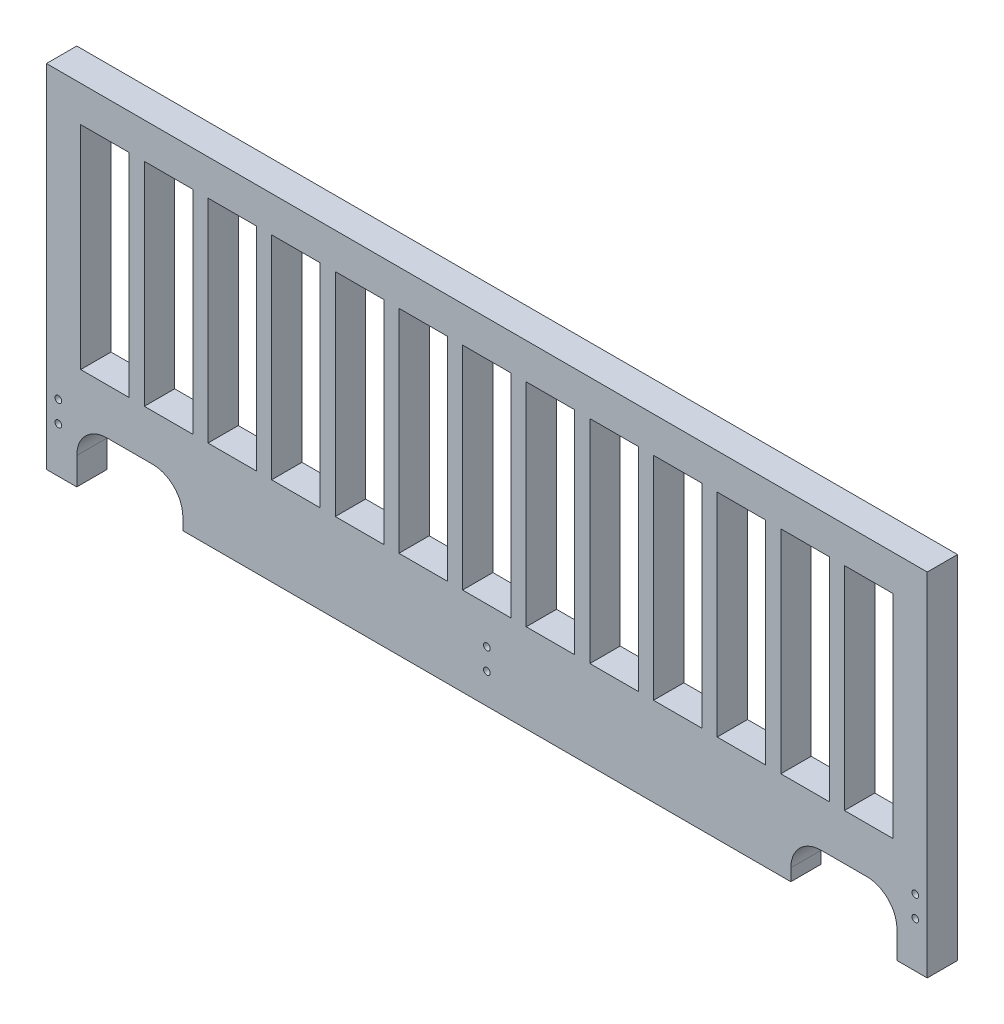
SolidWorks part; units mm, degrees
ref_plane "Plane1" through (0, 0, 0) normal (0, 0, 1) x (1, 0, 0)
ref_plane "Plane2" through (0, 0, 0) normal (0, 1, 0) x (1, 0, 0)
ref_plane "Plane3" through (0, 0, 0) normal (1, 0, 0) x (0, 0, -1)
sketch "Esquisse5" plane through (0, 0, 0) normal (0, 0, 1) x (1, 0, 0)
  line L0 (-55.5067, 0) -> (297.0702, 0) construction
  line L1 (-22.3043, 104.2) -> (297.0702, 104.2) construction
  line L2 (286.6703, -13.0084) -> (286.6703, 156.165) construction
  line L3 (-3.927, -63.8521) -> (-3.927, 156.165) construction
  line L4 (-19.0033, 19) -> (297.0702, 19) construction
  line L5 (-55.5067, 116) -> (297.0702, 116) construction
  line L6 (-22.3043, 34.2) -> (297.0702, 34.2) construction
  line L7 (-3.927, 116) -> (286.6703, 116)
  line L8 (-3.927, 116) -> (-3.927, 0)
  line L9 (16.073, 19) -> (31.073, 19)
  line L10 (286.6703, 116) -> (286.6733, 0)
  line L11 (7.373, 134.7083) -> (7.373, 31.2761) construction
  line L12 (275.3703, 134.7083) -> (275.3703, 31.2761) construction
  line L13 (23.373, 134.7083) -> (23.373, 31.2761) construction
  line L14 (28.373, 134.7083) -> (28.373, 31.2761) construction
  line L15 (28.373, 104.2) -> (44.373, 104.2)
  line L16 (7.373, 104.2) -> (23.373, 104.2)
  line L17 (7.373, 104.2) -> (7.373, 34.2)
  line L18 (7.373, 34.2) -> (23.373, 34.2)
  line L19 (23.373, 104.2) -> (23.373, 34.2)
  line L20 (28.373, 104.2) -> (28.373, 34.2)
  line L21 (28.373, 34.2) -> (44.373, 34.2)
  line L22 (44.373, 104.2) -> (44.373, 34.2)
  line L23 (49.373, 104.2) -> (65.373, 104.2)
  line L24 (49.373, 104.2) -> (49.373, 34.2)
  line L25 (49.373, 34.2) -> (65.373, 34.2)
  line L26 (65.373, 104.2) -> (65.373, 34.2)
  line L27 (70.373, 104.2) -> (86.373, 104.2)
  line L28 (70.373, 104.2) -> (70.373, 34.2)
  line L29 (70.373, 34.2) -> (86.373, 34.2)
  line L30 (86.373, 104.2) -> (86.373, 34.2)
  line L31 (91.373, 104.2) -> (107.373, 104.2)
  line L32 (91.373, 104.2) -> (91.373, 34.2)
  line L33 (91.373, 34.2) -> (107.373, 34.2)
  line L34 (107.373, 104.2) -> (107.373, 34.2)
  line L35 (112.373, 104.2) -> (128.373, 104.2)
  line L36 (112.373, 104.2) -> (112.373, 34.2)
  line L37 (112.373, 34.2) -> (128.373, 34.2)
  line L38 (128.373, 104.2) -> (128.373, 34.2)
  line L39 (133.373, 104.2) -> (149.373, 104.2)
  line L40 (133.373, 104.2) -> (133.373, 34.2)
  line L41 (133.373, 34.2) -> (149.373, 34.2)
  line L42 (149.373, 104.2) -> (149.373, 34.2)
  line L43 (154.373, 104.2) -> (170.373, 104.2)
  line L44 (154.373, 104.2) -> (154.373, 34.2)
  line L45 (154.373, 34.2) -> (170.373, 34.2)
  line L46 (170.373, 104.2) -> (170.373, 34.2)
  line L47 (175.373, 104.2) -> (191.373, 104.2)
  line L48 (175.373, 104.2) -> (175.373, 34.2)
  line L49 (175.373, 34.2) -> (191.373, 34.2)
  line L50 (191.373, 104.2) -> (191.373, 34.2)
  line L51 (196.373, 104.2) -> (212.373, 104.2)
  line L52 (196.373, 104.2) -> (196.373, 34.2)
  line L53 (196.373, 34.2) -> (212.373, 34.2)
  line L54 (212.373, 104.2) -> (212.373, 34.2)
  line L55 (217.373, 104.2) -> (233.373, 104.2)
  line L56 (217.373, 104.2) -> (217.373, 34.2)
  line L57 (217.373, 34.2) -> (233.373, 34.2)
  line L58 (233.373, 104.2) -> (233.373, 34.2)
  line L59 (238.373, 104.2) -> (254.373, 104.2)
  line L60 (238.373, 104.2) -> (238.373, 34.2)
  line L61 (238.373, 34.2) -> (254.373, 34.2)
  line L62 (254.373, 104.2) -> (254.373, 34.2)
  line L63 (259.373, 104.2) -> (275.373, 104.2)
  line L64 (259.373, 104.2) -> (259.373, 34.2)
  line L65 (259.373, 34.2) -> (275.373, 34.2)
  line L66 (275.373, 104.2) -> (275.373, 34.2)
  line L67 (141.3732, -11.4846) -> (141.3732, 70.4336) construction
  line L68 (6.073, 27.5518) -> (6.073, -16.6672) construction
  line L69 (41.073, 27.5518) -> (41.073, -30.4182) construction
  line L70 (297.0702, 5) -> (33.8181, 5) construction
  line L71 (-3.927, 0) -> (6.073, 0)
  line L72 (6.073, 0) -> (6.073, 9)
  line L73 (41.073, 9) -> (41.073, 5)
  line L74 (251.6733, 19) -> (266.6733, 19)
  line L75 (241.6733, 9) -> (241.6733, 5)
  line L77 (276.6733, 0) -> (276.6733, 9)
  line L78 (286.6733, 0) -> (276.6733, 0)
  line L79 (41.073, 5) -> (241.6733, 5)
  circle A0 centre (0, 22) radius 1.1
  arc A1 (16.073, 19) -> (6.073, 9) centre (16.073, 9) ccw
  circle A2 centre (141.3732, 22) radius 1.1
  arc A3 (41.073, 9) -> (31.073, 19) centre (31.073, 9) ccw
  circle A4 centre (282.7433, 22) radius 1.1
  arc A5 (241.6733, 9) -> (251.6733, 19) centre (251.6733, 9) cw
  arc A6 (266.6733, 19) -> (276.6733, 9) centre (266.6733, 9) cw
  circle A7 centre (0, 15) radius 1.1
  circle A8 centre (141.3732, 15) radius 1.1
  circle A9 centre (282.7433, 15) radius 1.1
  point P99 (6.073, 19)
  point P102 (41.073, 19)
  dimension "D3" = 11.8
  dimension "D12" = 10
  dimension "D1" = 19
  dimension "D2" = 116
  dimension "D4" = 70
  dimension "D5" = 11.3
  dimension "D6" = 11.3
  dimension "D7" = 16
  dimension "D8" = 5
  dimension "D9" = 10
  dimension "D10" = 45
  dimension "D11" = 5
extrude "Extrusion1" add sketch "Esquisse5" along normal blind 10
